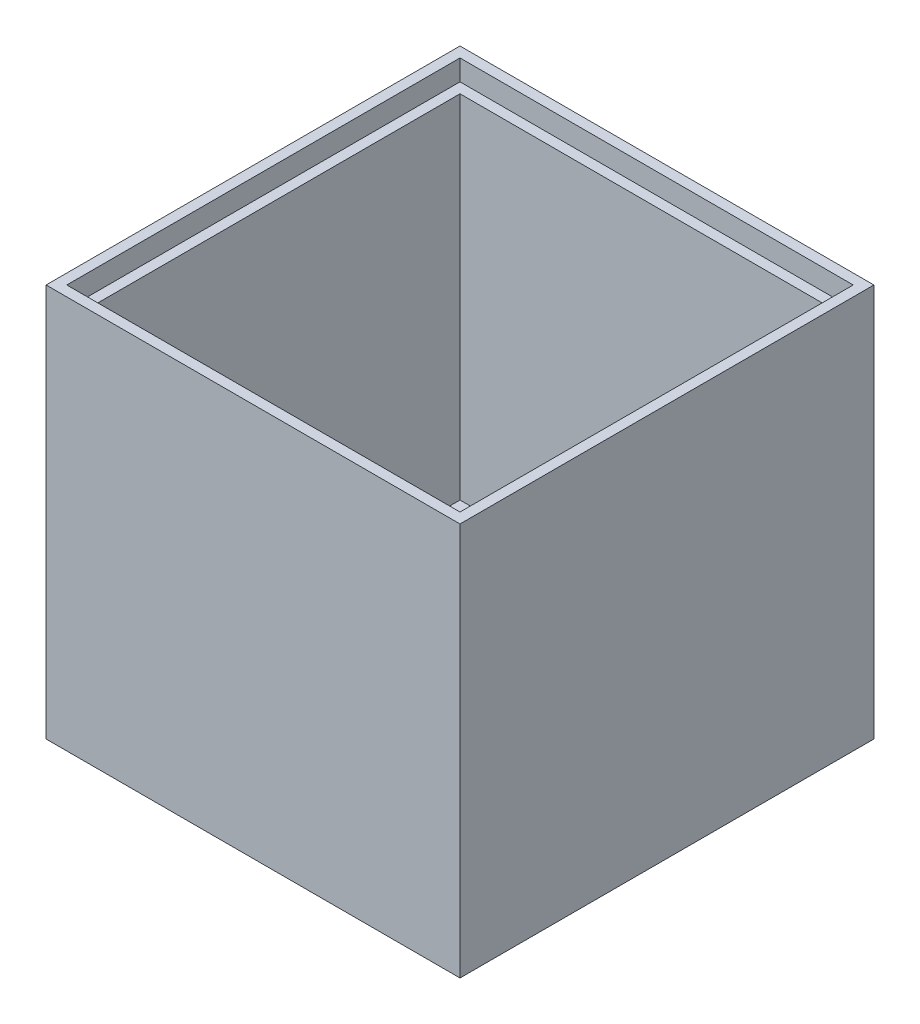
SolidWorks part; units mm, degrees
ref_plane "Front Plane" through (0, 0, 0) normal (0, 0, 1) x (1, 0, 0)
ref_plane "Top Plane" through (0, 0, 0) normal (0, 1, 0) x (1, 0, 0)
ref_plane "Right Plane" through (0, 0, 0) normal (1, 0, 0) x (0, 0, -1)
sketch "Sketch1" plane through (0, 0, 0) normal (0, 1, 0) x (1, 0, 0)
  line L1 (0, 0) -> (50.8, 0)
  line L2 (0, 0) -> (0, 50.8)
  line L3 (0, 50.8) -> (50.8, 50.8)
  line L4 (50.8, 0) -> (50.8, 50.8)
  dimension "D1" = 50.8
extrude "Boss-Extrude1" add sketch "Sketch1" along normal blind 48.26
sketch "Sketch2" plane through (0, 48.26, 0) normal (0, 1, 0) x (1, 0, 0)
  line L0 (0, 0) -> (50.8, 0) construction
  line L1 (48.26, 2.54) -> (2.54, 2.54)
  line L2 (48.26, 2.54) -> (48.26, 48.26)
  line L3 (48.26, 48.26) -> (2.54, 48.26)
  line L4 (2.54, 2.54) -> (2.54, 48.26)
  line L6 (0, 50.8) -> (0, 0) construction
  dimension "D1" = 45.72
  dimension "D2" = 2.54
  dimension "D3" = 2.54
extrude "Cut-Extrude1" cut sketch "Sketch2" against normal blind 45.72
sketch "Sketch3" plane through (0, 48.26, 0) normal (0, 1, 0) x (1, 0, 0)
  line L0 (0, 50.8) -> (0, 0) construction
  line L1 (1.27, 49.53) -> (49.53, 49.53)
  line L2 (1.27, 49.53) -> (1.27, 1.27)
  line L3 (1.27, 1.27) -> (49.53, 1.27)
  line L4 (49.53, 49.53) -> (49.53, 1.27)
  line L5 (0, 0) -> (50.8, 0) construction
  line L6 (50.8, 0) -> (50.8, 50.8) construction
  point P8 (49.0845, 1.27)
  dimension "D1" = 1.27
  dimension "D2" = 1.27
  dimension "D3" = 1.27
extrude "Cut-Extrude2" cut sketch "Sketch3" against normal blind 2.54
